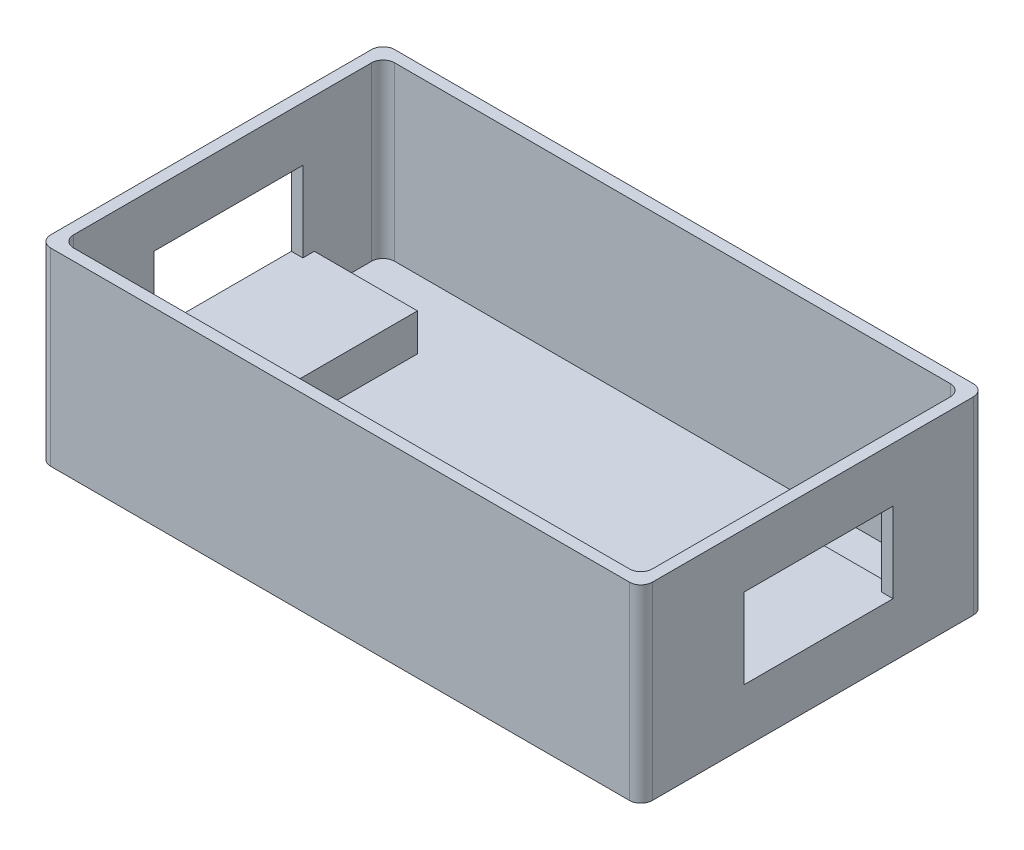
SolidWorks part; units mm, degrees
ref_plane "Plan de face" through (0, 0, 0) normal (0, 0, 1) x (1, 0, 0)
ref_plane "Plan de dessus" through (0, 0, 0) normal (0, 1, 0) x (1, 0, 0)
ref_plane "Plan de droite" through (0, 0, 0) normal (1, 0, 0) x (0, 0, -1)
sketch "Esquisse2" plane through (0, 0, 0) normal (0, 1, 0) x (1, 0, 0)
  line L0 (0, 30) -> (-52.5, 30)
  line L1 (0, -55) -> (0, 55) construction
  line L2 (0, 30) -> (52.5, 30)
  line L3 (-52.5, 30) -> (-52.5, -30)
  line L4 (-55, 0) -> (55, 0) construction
  line L5 (52.5, 30) -> (52.5, -30)
  line L6 (0, -30) -> (52.5, -30)
  line L7 (0, -30) -> (-52.5, -30)
  point P10 (52.5, 0)
  point P11 (-52.5, 0)
  dimension "D1" = 52.5
  dimension "D2" = 52.5
  dimension "D3" = 30
  dimension "D4" = 30
extrude "Boss.-Extru.1" add sketch "Esquisse2" along normal blind 3
sketch "Esquisse3" plane through (0, 3, 0) normal (0, 1, 0) x (1, 0, 0)
  line L1 (-50.5, 28) -> (50.5, 28)
  line L2 (-50.5, 28) -> (-50.5, -28)
  line L3 (-50.5, -28) -> (50.5, -28)
  line L4 (50.5, 28) -> (50.5, -28)
  line L5 (-52.5, 30) -> (52.5, 30)
  line L6 (-52.5, 30) -> (-52.5, -30)
  line L7 (-52.5, -30) -> (52.5, -30)
  line L8 (52.5, 30) -> (52.5, -30)
  dimension "D1" = 2
  dimension "D2" = 2
  dimension "D3" = 2
  dimension "D4" = 2
extrude "Boss.-Extru.2" add sketch "Esquisse3" along normal blind 30
fillet "Congé2" radius 2 4 edges at (-52.5, 16.5, 30) (52.5, 16.5, 30) (52.5, 16.5, -30) (-52.5, 16.5, -30)
fillet "Congé4" radius 2 4 edges at (-50.5, 18, 28) (50.5, 18, 28) (-50.5, 18, -28) (50.5, 18, -28)
sketch "Esquisse4" plane through (-52.5, 0, 0) normal (-1, 0, 0) x (0, 0, 1)
  line L1 (-14, 23.5) -> (12, 23.5)
  line L2 (-14, 23.5) -> (-14, 9.5)
  line L3 (-14, 9.5) -> (12, 9.5)
  line L4 (12, 23.5) -> (12, 9.5)
  line L7 (-28, 33) -> (28, 33) construction
  line L9 (-30, 0) -> (-30, 33) construction
  dimension "D1" = 14
  dimension "D2" = 26
  dimension "D3" = 9.5
  dimension "D5" = 16
extrude "Enlèv. mat.-Extru.2" cut sketch "Esquisse4" against normal blind 162
sketch "Esquisse6" plane through (0, 3, 0) normal (0, 1, 0) x (1, 0, 0)
  line L0 (-50.5, 26) -> (-50.5, -26) construction
  line L1 (-50.5, 16) -> (-32.5, 16)
  line L2 (-50.5, 16) -> (-50.5, -14)
  line L3 (-50.5, -14) -> (-32.5, -14)
  line L4 (-32.5, 16) -> (-32.5, -14)
  line L5 (48.5, 28) -> (-48.5, 28) construction
  dimension "D1" = 18
  dimension "D2" = 30
  dimension "D3" = 12
extrude "Boss.-Extru.7" add sketch "Esquisse6" along normal blind 6.5
mirror "Symétrie1" about plane through (0, 0, 0) normal (1, 0, 0) of "Boss.-Extru.7"
